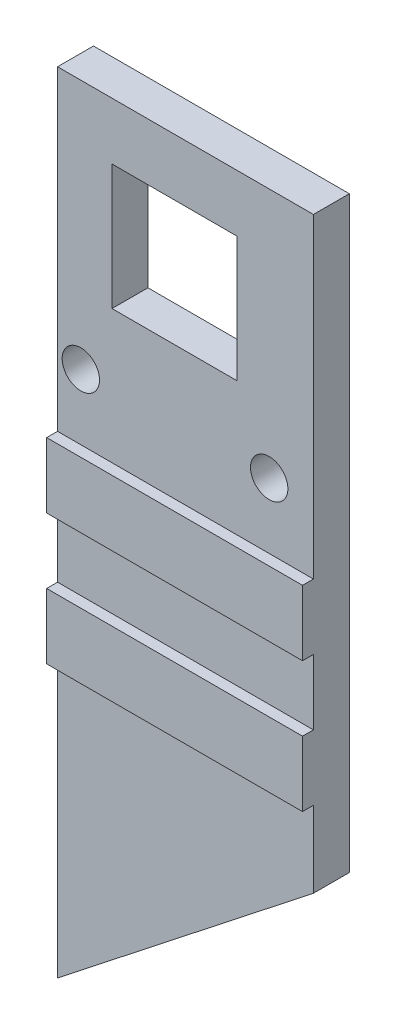
SolidWorks part; units mm, degrees
ref_plane "前基準面" through (0, 0, 0) normal (0, 0, 1) x (1, 0, 0)
ref_plane "上基準面" through (0, 0, 0) normal (0, 1, 0) x (1, 0, 0)
ref_plane "右基準面" through (0, 0, 0) normal (1, 0, 0) x (0, 0, -1)
sketch "草圖1" plane through (0, 0, 0) normal (0, 0, 1) x (1, 0, 0)
  line L1 (-15.254, 33.1662) -> (-15.254, -17.8338)
  line L2 (15.254, 33.1662) -> (15.254, -17.8338)
  line L4 (-5.7877, 27.9319) -> (5.7123, 27.9319)
  line L5 (-5.7877, 27.9319) -> (-5.7877, 19.0094)
  line L7 (5.7123, 27.9319) -> (5.7123, 19.0094)
  line L8 (0, 33.1662) -> (0, 8.7242) construction
  line L9 (-15.254, 2.1662) -> (15.254, 2.1662)
  line L10 (-15.254, 2.1662) -> (-15.254, -3.8338)
  line L11 (-15.254, -3.8338) -> (15.254, -3.8338)
  line L12 (15.254, 2.1662) -> (15.254, -3.8338)
  line L13 (-15.254, -11.8338) -> (15.254, -11.8338)
  line L14 (-15.254, -11.8338) -> (-15.254, -17.8338)
  line L15 (-15.254, -17.8338) -> (15.254, -17.8338)
  line L16 (15.254, -11.8338) -> (15.254, -17.8338)
  line L18 (-15.254, 33.1662) -> (-15.254, -17.8338)
  line L19 (-15.254, -17.8338) -> (15.254, -17.8338)
  line L20 (15.254, 33.1662) -> (15.254, -17.8338)
  line L21 (-15.254, -17.8338) -> (-15.254, -42.8338)
  line L23 (-5.7877, 19.0094) -> (-5.7877, 16.4319)
  line L24 (-5.7877, 16.4319) -> (5.7123, 16.4319)
  line L25 (5.7123, 19.0094) -> (5.7123, 16.4319)
  line L26 (-15.254, 33.1662) -> (15.254, 33.1662)
  line L27 (-15.254, -42.8338) -> (15.254, -42.8338)
  line L28 (15.254, -42.8338) -> (15.254, -17.8338)
  line L30 (-12.254, -20.8338) -> (12.254, -20.8338)
  line L31 (-12.254, -20.8338) -> (-12.254, -39.8338)
  line L32 (-12.254, -39.8338) -> (12.254, -39.8338)
  line L33 (12.254, -20.8338) -> (12.254, -39.8338)
  circle A0 centre (-8.65, 10.1662) radius 1.7161
  circle A1 centre (8.65, 10.1662) radius 1.7161
  dimension "D8" = 3
  dimension "D1" = 6
  dimension "D2" = 11.5
  dimension "D3" = 8
  dimension "D4" = 8
  dimension "D5" = 6
  dimension "D6" = 11.5
  dimension "D7" = 76
  dimension "D9" = 3
  dimension "D10" = 23
  dimension "D11" = 3
  dimension "D12" = 3
extrude "填料-伸長1" add sketch "草圖1" along normal blind 3.3 contours L8 L26 L1 L9 L24 L23 L5 L4 A0 | L26 L8 L4 L7 L25 L24 L9 L2 A1 | L8 L15 L21 L27 L32 L31 L30 | L19 L8 L30 L33 L32 L27 L28 | L8 L9 L1 L11 | L8 L13 L1 L15 | L13 L8 L19 L2 | L9 L8 L11 L2 | L8 L11 L1 L13 | L11 L8 L13 L2
sketch "草圖2" plane through (0, 0, 3.3) normal (0, 0, 1) x (1, 0, 0)
  line L0 (-15.254, 33.1662) -> (-15.254, -42.8338) construction
  line L1 (-15.254, 4.1662) -> (15.254, 4.1662)
  line L2 (-15.254, 4.1662) -> (-15.254, -1.8338)
  line L3 (-15.254, -1.8338) -> (15.254, -1.8338)
  line L4 (15.254, 4.1662) -> (15.254, -1.8338)
  line L5 (15.254, -42.8338) -> (15.254, 33.1662) construction
  line L7 (-15.254, -7.8338) -> (15.254, -7.8338)
  line L8 (-15.254, -7.8338) -> (-15.254, -13.8338)
  line L9 (-15.254, -13.8338) -> (15.254, -13.8338)
  line L10 (15.254, -7.8338) -> (15.254, -13.8338)
  circle A0 centre (-8.65, 10.1662) radius 1.7161 construction
  dimension "D1" = 6
  dimension "D2" = 6
  dimension "D3" = 6
  dimension "D4" = 6
extrude "填料-伸長2" add sketch "草圖2" along normal blind 1
sketch "草圖3" plane through (0, 0, 0) normal (0, 0, 1) x (1, 0, 0)
  line L0 (15.254, -42.8338) -> (-15.254, -18.4741)
  line L1 (-15.254, -13.8338) -> (-15.254, -42.8338) construction
  line L2 (-15.254, -18.4741) -> (15.254, -18.4741)
  line L3 (15.254, -42.8338) -> (15.254, -13.8338) construction
  line L4 (15.254, -18.4741) -> (15.254, -42.8338)
extrude "填料-伸長3" add sketch "草圖3" along normal blind 3.3
sketch "草圖4" plane through (0, 0, 3.3) normal (0, 0, 1) x (1, 0, 0)
  line L0 (15.254, -42.8338) -> (-15.254, -18.8067)
  line L1 (-15.254, -13.8338) -> (-15.254, -42.8338) construction
  line L2 (-15.254, -18.8067) -> (-15.254, -42.8338)
  line L3 (-15.254, -42.8338) -> (15.254, -42.8338)
extrude "除料-伸長1" cut sketch "草圖4" against normal blind 3.3
sketch "草圖8" plane through (0, 0, 3.3) normal (0, 0, 1) x (1, 0, 0)
  line L1 (-15.254, -13.8338) -> (15.254, -13.8338)
  line L2 (-15.254, -13.8338) -> (-15.254, -42.8338)
  line L3 (-15.254, -42.8338) -> (15.254, -42.8338)
  line L4 (15.254, -13.8338) -> (15.254, -42.8338)
extrude "填料-伸長5" add sketch "草圖8" against normal blind 3.3
sketch "草圖9" plane through (0, 0, 3.3) normal (0, 0, 1) x (1, 0, 0)
  line L0 (-15.254, -42.8338) -> (15.254, -18.8338)
  line L1 (15.254, -42.8338) -> (15.254, -13.8338) construction
  line L2 (15.254, -18.8338) -> (15.254, -42.8338)
  line L3 (15.254, -42.8338) -> (-15.254, -42.8338)
  dimension "D1" = 5
extrude "除料-伸長3" cut sketch "草圖9" against normal blind 3.3 contours L3 L0 L2
sketch "草圖12" plane through (0, 0, 4.3) normal (0, 0, 1) x (1, 0, 0)
  line L0 (-15.254, 33.1662) -> (15.254, 33.1662) construction
  line L1 (-15.254, 33.1662) -> (-10.7877, 33.1662)
  line L2 (-15.254, 33.1662) -> (-15.254, -43.1307)
  line L3 (-15.254, -43.1307) -> (-10.7877, -43.1307)
  line L4 (-10.7877, 33.1662) -> (-10.7877, -43.1307)
  line L5 (12.7123, 33.1662) -> (16.6246, 33.1662)
  line L6 (12.7123, 33.1662) -> (12.7123, -22.686)
  line L7 (12.7123, -22.686) -> (16.6246, -22.686)
  line L8 (16.6246, 33.1662) -> (16.6246, -22.686)
  line L9 (-5.7877, 27.9319) -> (-5.7877, 16.4319) construction
  line L10 (5.7123, 27.9319) -> (5.7123, 16.4319) construction
  dimension "D1" = 5
  dimension "D2" = 7
extrude "除料-伸長6" cut sketch "草圖12" against normal blind 11.3
